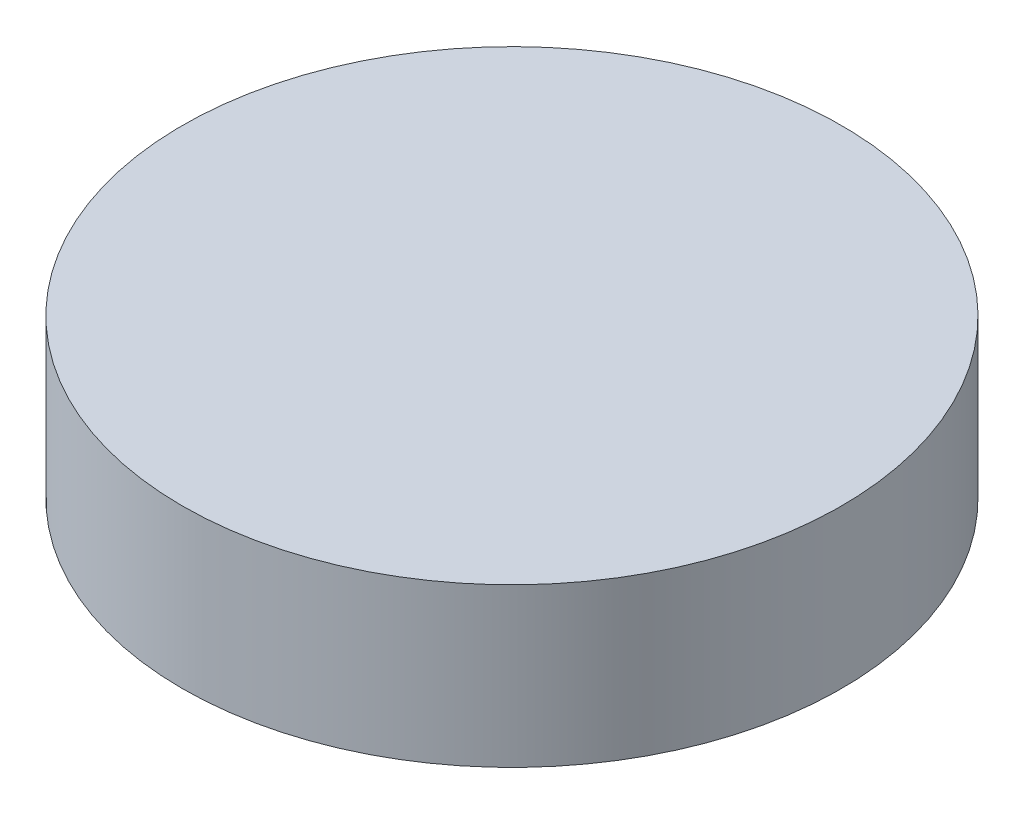
SolidWorks part; units mm, degrees
ref_plane "前视基准面" through (0, 0, 0) normal (0, 0, 1) x (1, 0, 0)
ref_plane "上视基准面" through (0, 0, 0) normal (0, 1, 0) x (1, 0, 0)
ref_plane "右视基准面" through (0, 0, 0) normal (1, 0, 0) x (0, 0, -1)
sketch "草图1" plane through (0, 0, 0) normal (0, 1, 0) x (1, 0, 0)
  circle A0 centre (0, 0) radius 6.25
  dimension "D1" = 12.5
extrude "凸台-拉伸1" add sketch "草图1" along normal blind 3
